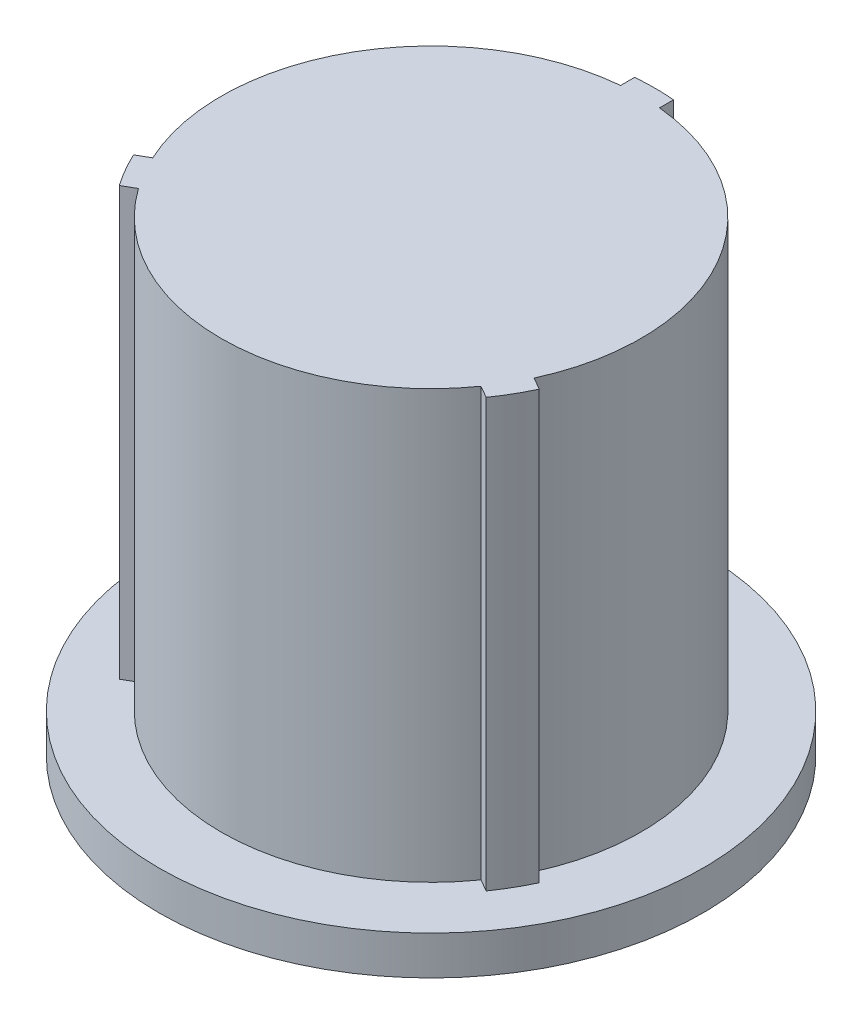
SolidWorks part; units mm, degrees
ref_plane "Front Plane" through (0, 0, 0) normal (0, 0, 1) x (1, 0, 0)
ref_plane "Top Plane" through (0, 0, 0) normal (0, 1, 0) x (1, 0, 0)
ref_plane "Right Plane" through (0, 0, 0) normal (1, 0, 0) x (0, 0, -1)
sketch "Sketch1" plane through (0, 0, 0) normal (0, 1, 0) x (1, 0, 0)
  line L0 (-0.7938, 9.1095) -> (-0.7938, 8.5357)
  line L1 (0.7937, 9.1095) -> (0.7937, 8.5357)
  line L2 (8.2859, -3.8673) -> (7.789, -3.5804)
  line L3 (7.4922, -5.2421) -> (6.9952, -4.9552)
  line L4 (-7.4922, -5.2421) -> (-6.9952, -4.9552)
  line L5 (-8.2859, -3.8673) -> (-7.789, -3.5804)
  arc A0 (-6.9952, -4.9552) -> (6.9952, -4.9552) centre (0, 0) ccw
  arc A1 (-8.2859, -3.8673) -> (-7.4922, -5.2421) centre (0, 0) ccw
  arc A2 (0.7937, 9.1095) -> (-0.7938, 9.1095) centre (0, 0) ccw
  arc A3 (7.4922, -5.2421) -> (8.2859, -3.8673) centre (0, 0) ccw
  arc A4 (7.789, -3.5804) -> (0.7937, 8.5357) centre (0, 0) ccw
  arc A5 (-0.7938, 8.5357) -> (-7.789, -3.5804) centre (0, 0) ccw
  point P18 (0, 0)
  dimension "D1" = 17.145
  dimension "D2" = 18.288
  dimension "D3" = 1.5875
  dimension "D4" = 3
extrude "Boss-Extrude1" add sketch "Sketch1" along normal blind 19.05
sketch "Sketch6" plane through (0, 0, 0) normal (1, 0, 0) x (0, 0, -1)
  line L0 (8.5357, 1.5875) -> (9.144, 1.5875)
  line L1 (8.5357, 1.5875) -> (8.5357, 0)
  line L3 (8.5357, 0) -> (9.144, 0)
  line L5 (9.144, 0) -> (9.144, 1.5875)
  line L6 (0, 19.7302) -> (0, -0.9338) construction
  dimension "D1" = 1.5875
revolve "Cut-Revolve2" cut sketch "Sketch6" angle 360 about L6
sketch "Sketch8" plane through (0, 0, 0) normal (1, 0, 0) x (0, 0, -1)
  line L1 (8.5357, 1.5875) -> (11.1125, 1.5875)
  line L2 (8.5357, 1.5875) -> (8.5357, 0)
  line L3 (8.5357, 0) -> (11.1125, 0)
  line L4 (11.1125, 1.5875) -> (11.1125, 0)
  line L8 (0, 4.4839) -> (0, -1.895) construction
  dimension "D1" = 11.1125
revolve "Revolve2" add sketch "Sketch8" angle 360 about L8
